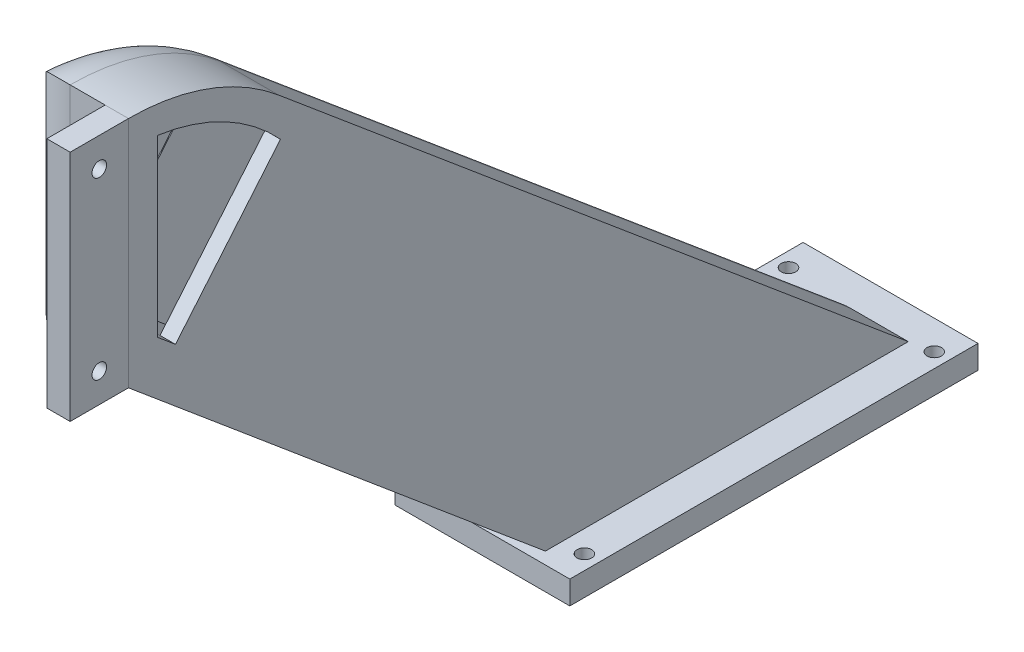
SolidWorks part; units mm, degrees
ref_plane "Front Plane" through (0, 0, 0) normal (0, 0, 1) x (1, 0, 0)
ref_plane "Top Plane" through (0, 0, 0) normal (0, 1, 0) x (1, 0, 0)
ref_plane "Right Plane" through (0, 0, 0) normal (1, 0, 0) x (0, 0, -1)
sketch "Sketch1" plane through (0, 0, 0) normal (1, 0, 0) x (0, 0, -1)
  line L0 (0, 0) -> (10, 0)
  line L5 (0, 20) -> (10, 20)
  line L6 (0, 20) -> (0, -20)
  line L7 (0, -20) -> (10, -20)
  line L8 (10, 20) -> (10, -20)
  circle A1 centre (5, 15) radius 1.25
  circle A2 centre (5, -15) radius 1.25
  point P4 (0, 0)
  point P13 (5, 0)
  point P14 (0, 0)
  dimension "D1" = 2.5
  dimension "D2" = 40
  dimension "D3" = 10
  dimension "D4" = 15
extrude "Boss-Extrude1" add sketch "Sketch1" along normal blind 4 contours L8 L0 L6 L7 A2 | L8 L5 L6 L0 A1
sketch "Sketch2" plane through (4, 0, 0) normal (1, 0, 0) x (0, 0, -1)
  line L0 (10, -20) -> (81.5052, -80)
  line L1 (0, 20) -> (10, 20) construction
  line L2 (35.7115, 10.6418) -> (143.7342, -80)
  line L3 (0, -20) -> (10, -20) construction
  line L4 (81.5052, -80) -> (143.7342, -80)
  line L5 (10, 20) -> (10, -20)
  arc A0 (10, 20) -> (35.7115, 10.6418) centre (10, -20) cw
  line M3 (10, -20) -> (10, 20)
  dimension "D3" = 40
  dimension "D1" = 60
  dimension "D2" = 140
extrude "Boss-Extrude2" add sketch "Sketch2" against normal blind 20 separate body contours A0 L0 L4 L2 M3
fillet "Fillet2" radius 10 4 edges at (-16, -34.6791, -89.7228) (-16, -50, -45.7526) (-16, 0, -10) (-16, 17.5877, -23.6808)
sketch "Sketch3" plane through (4, 0, 0) normal (1, 0, 0) x (0, 0, -1)
  line L0 (15, 15) -> (15, -15)
  line L1 (15, -15) -> (18.0642, -17.5712)
  line L2 (18.0642, -17.5712) -> (36.0677, 3.8846)
  line L3 (10, -20) -> (81.5052, -80) construction
  arc A0 (15, 15) -> (36.0677, 3.8846) centre (10, -20) cw
  arc A1 (35.7115, 10.6418) -> (10, 20) centre (10, -20) ccw construction
  circle A2 centre (5, -15) radius 1.25
  circle A5 centre (5, 15) radius 1.25
  dimension "D1" = 10
  dimension "D2" = 4
extrude "Cut-Extrude1" cut sketch "Sketch3" against normal blind 15
sketch "Sketch4" plane through (0, -16.1548, -19.2526) normal (0, 0.6428, 0.766) x (1, 0, 0)
  line L1 (-10.8599, -1.8555) -> (1.3457, -1.8555)
  line L2 (-10.8599, -1.8555) -> (-10.8599, 26.4192)
  line L3 (-10.8599, 26.4192) -> (1.3457, 26.4192)
  line L4 (1.3457, -1.8555) -> (1.3457, 26.4192)
extrude "Cut-Extrude2" cut sketch "Sketch4" against normal through all
sketch "Sketch5" plane through (0, -80, 0) normal (0, -1, 0) x (1, 0, 0)
  line L1 (-19.7571, -79.4475) -> (10.2429, -79.4475)
  line L2 (-19.7571, -79.4475) -> (-19.7571, -149.4475)
  line L3 (-19.7571, -149.4475) -> (10.2429, -149.4475)
  line L4 (10.2429, -79.4475) -> (10.2429, -149.4475)
  line L5 (-19.7571, -79.4475) -> (10.2429, -149.4475) construction
  line L6 (-19.7571, -149.4475) -> (10.2429, -79.4475) construction
  line L7 (-10.8599, -92.4536) -> (-10.8599, -136.4413) construction
  line L8 (1.3457, -92.4536) -> (-10.8599, -92.4536) construction
  line L9 (-4.7571, -79.4475) -> (-4.7571, -149.4475) construction
  line L10 (-19.7571, -114.4475) -> (10.2429, -114.4475) construction
  line L13 (-10.8599, -92.4536) -> (1.3457, -92.4536)
  line L14 (-10.8599, -92.4536) -> (-10.8599, -136.4413)
  line L15 (-10.8599, -136.4413) -> (1.3457, -136.4413)
  line L16 (1.3457, -92.4536) -> (1.3457, -136.4413)
  line L17 (-10.8599, -92.4536) -> (1.3457, -136.4413) construction
  line L18 (-10.8599, -136.4413) -> (1.3457, -92.4536) construction
  circle A0 centre (-17.2571, -84.4475) radius 1.25
  circle A1 centre (7.7429, -84.4475) radius 1.25
  circle A2 centre (7.7429, -144.4475) radius 1.25
  circle A3 centre (-17.2571, -144.4475) radius 1.25
  point P0 (-4.7571, -114.4475)
  point P10 (-10.8599, -114.4475)
  point P13 (-4.7571, -92.4536)
  point P20 (-4.7571, -114.4475)
  dimension "D1" = 2.5
  dimension "D2" = 70
  dimension "D3" = 30
  dimension "D4" = 30
  dimension "D5" = 12.5
extrude "Boss-Extrude3" add sketch "Sketch5" along normal blind 4
